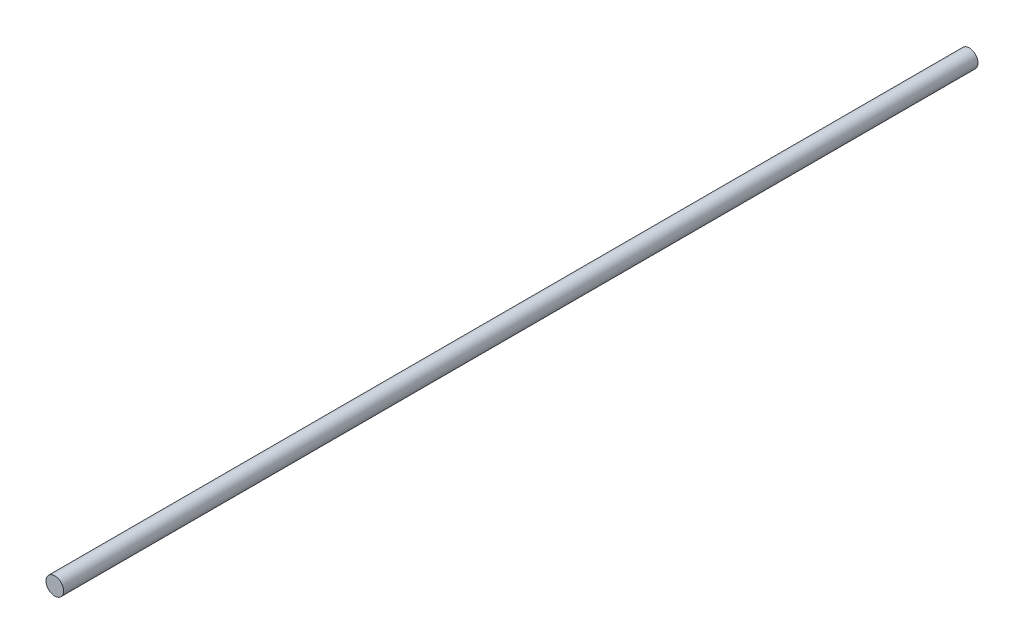
SolidWorks part; units mm, degrees
ref_plane "Front Plane" through (0, 0, 0) normal (0, 0, 1) x (1, 0, 0)
ref_plane "Top Plane" through (0, 0, 0) normal (0, 1, 0) x (1, 0, 0)
ref_plane "Right Plane" through (0, 0, 0) normal (1, 0, 0) x (0, 0, -1)
sketch "Sketch1" plane through (0, 0, 0) normal (0, 0, 1) x (1, 0, 0)
  circle A0 centre (0, 0) radius 2.5
  dimension "D1" = 5
extrude "Boss-Extrude1" add sketch "Sketch1" along normal blind 260
